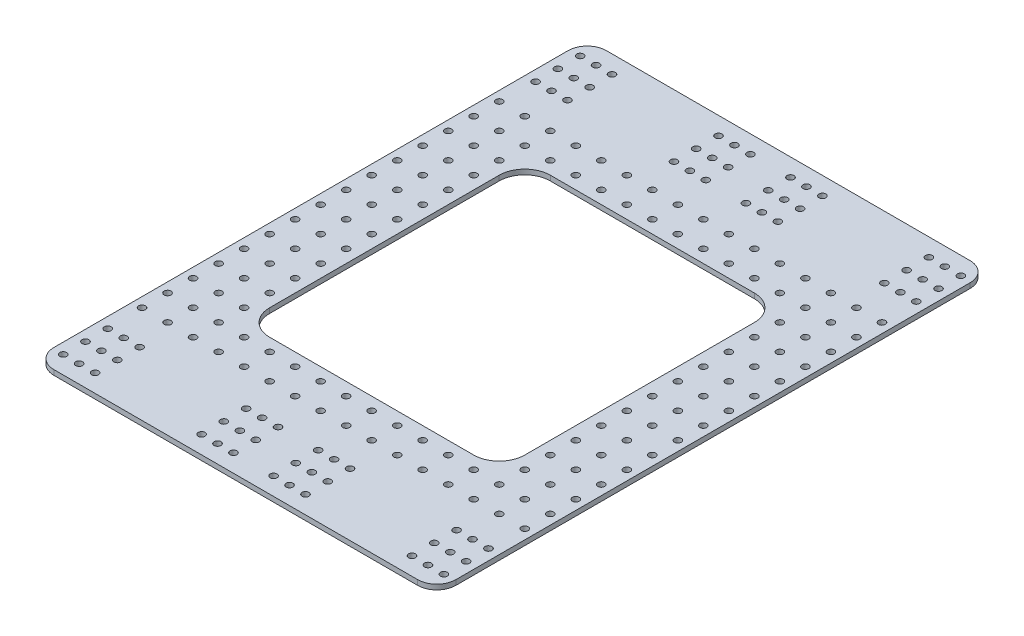
SolidWorks part; units mm, degrees
ref_plane "Front Plane" through (0, 0, 0) normal (0, 0, 1) x (1, 0, 0)
ref_plane "Top Plane" through (0, 0, 0) normal (0, 1, 0) x (1, 0, 0)
ref_plane "Right Plane" through (0, 0, 0) normal (1, 0, 0) x (0, 0, -1)
sketch "Sketch2" plane through (0, 50, 0) normal (0, 1, 0) x (1, 0, 0)
  line L6 (100.0588, 137.5) -> (-100.0588, 137.5)
  line L7 (100.0588, 137.5) -> (100.0588, -137.5)
  line L8 (100.0588, -137.5) -> (-100.0588, -137.5)
  line L9 (-100.0588, 137.5) -> (-100.0588, -137.5)
  line L10 (100.0588, 137.5) -> (-100.0588, -137.5) construction
  line L11 (100.0588, -137.5) -> (-100.0588, 137.5) construction
  point P0 (0, 0)
extrude "Boss-Extrude1" add sketch "Sketch2" along normal blind 2.5
sketch "Sketch4" plane through (0, 52.5, 0) normal (0, 1, 0) x (1, 0, 0)
  circle A0 centre (-9.9812, -128.65) radius 1.27 construction
  circle A1 centre (-9.9812, -106.4725) radius 1.27 construction
  circle A2 centre (-9.9812, -117.5612) radius 1.27 construction
  circle A3 centre (-17.9187, -117.5612) radius 1.27 construction
  circle A4 centre (-17.9187, -106.4725) radius 1.27 construction
  circle A5 centre (-25.8562, -106.4725) radius 1.27 construction
  circle A6 centre (-25.8562, -117.5612) radius 1.27 construction
  circle A7 centre (-17.9187, -128.65) radius 1.27 construction
  circle A8 centre (-25.8562, -128.65) radius 1.27 construction
  circle A9 centre (-86.8122, -117.5612) radius 1.27 construction
  circle A10 centre (-86.8122, -128.65) radius 1.27 construction
  circle A11 centre (-78.8747, -128.65) radius 1.27 construction
  circle A12 centre (-78.8747, -117.5612) radius 1.27 construction
  circle A13 centre (-78.8747, -106.4725) radius 1.27 construction
  circle A14 centre (-86.8122, -106.4725) radius 1.27 construction
  circle A15 centre (-94.7497, -106.4725) radius 1.27 construction
  circle A16 centre (-94.7497, -117.5612) radius 1.27 construction
  circle A17 centre (-94.7497, -128.65) radius 1.27 construction
  circle A18 centre (-9.9812, -128.65) radius 1.27 construction
  circle A19 centre (-9.9812, -106.4725) radius 1.27 construction
  circle A20 centre (-9.9812, -117.5612) radius 1.27 construction
  circle A21 centre (-17.9187, -117.5612) radius 1.27 construction
  circle A22 centre (-17.9187, -106.4725) radius 1.27 construction
  circle A23 centre (-25.8562, -106.4725) radius 1.27 construction
  circle A24 centre (-25.8562, -117.5612) radius 1.27 construction
  circle A25 centre (-17.9187, -128.65) radius 1.27 construction
  circle A26 centre (-25.8562, -128.65) radius 1.27 construction
  circle A27 centre (-86.8122, -117.5612) radius 1.27 construction
  circle A28 centre (-86.8122, -128.65) radius 1.27 construction
  circle A29 centre (-78.8747, -128.65) radius 1.27 construction
  circle A30 centre (-78.8747, -117.5612) radius 1.27 construction
  circle A31 centre (-78.8747, -106.4725) radius 1.27 construction
  circle A32 centre (-86.8122, -106.4725) radius 1.27 construction
  circle A33 centre (-94.7497, -106.4725) radius 1.27 construction
  circle A34 centre (-94.7497, -117.5612) radius 1.27 construction
  circle A35 centre (-94.7497, -128.65) radius 1.27 construction
hole_wizard "M3 Clearance Hole1" positions "3DSketch2" profile "Sketch6" hole size "M3" standard "ANSI Metric" end condition through all
sketch3d "3DSketch2"
  point P0 (-94.7497, 52.5, 106.4725)
  point P3 (-86.8122, 52.5, 106.4725)
  point P6 (-78.8747, 52.5, 106.4725)
  point P9 (-78.8747, 52.5, 117.5612)
  point P12 (-86.8122, 52.5, 117.5612)
  point P15 (-94.7497, 52.5, 117.5612)
  point P18 (-94.7497, 52.5, 128.65)
  point P21 (-86.8122, 52.5, 128.65)
  point P24 (-78.8747, 52.5, 128.65)
  point P27 (-25.8562, 52.5, 106.4725)
  point P30 (-17.9187, 52.5, 106.4725)
  point P33 (-9.9812, 52.5, 106.4725)
  point P35 (-9.9812, 52.5, 117.5612)
  point P38 (-17.9187, 52.5, 117.5612)
  point P41 (-25.8562, 52.5, 117.5612)
  point P44 (-25.8562, 52.5, 128.65)
  point P47 (-17.9187, 52.5, 128.65)
  point P50 (-9.9812, 52.5, 128.65)
sketch "Sketch6" plane through (-94.7497, 52.5, 106.4725) normal (1, 0, 0) x (0, 0, 1)
  line L0 (0, 0) -> (0, 2.5)
  line L1 (0, 2.5) -> (1.7, 2.5)
  line L2 (1.7, 2.5) -> (1.7, 0)
  line L5 (1.7, 0) -> (0, 0)
  line L11 (0, -6.35) -> (0, 107.95) construction
  dimension "Thru Hole Dia." = 3.4
  dimension "Thru Hole Depth" = 2.5
mirror "Mirror1" about plane through (0, 0, 0) normal (1, 0, 0) of "M3 Clearance Hole1"
mirror "Mirror2" about plane through (0, 0, 0) normal (0, 0, 1) of "M3 Clearance Hole1", "Mirror1"
fillet "Fillet1" radius 9.525 4 edges at (-100.0588, 51.25, -137.5) (100.0588, 51.25, 137.5) (-100.0588, 51.25, 137.5) (100.0588, 51.25, -137.5)
sketch "Sketch7" plane through (0, 52.5, 0) normal (0, 1, 0) x (1, 0, 0)
  line L1 (0, 0) -> (6.35, 0) construction
  line L2 (0, 0) -> (0, -6.35) construction
  line L3 (0, -6.35) -> (6.35, -6.35) construction
  line L4 (6.35, 0) -> (6.35, -6.35) construction
  point P6 (6.35, -6.35)
  dimension "D1" = 6.35
hole_wizard "M3 Clearance Hole2" positions "Sketch9" profile "Sketch10" hole size "M3" standard "ANSI Metric" end condition through all
sketch "Sketch9" plane through (0, 52.5, 0) normal (0, 1, 0) x (1, 0, 0)
  point P0 (6.35, 0)
sketch "Sketch10" plane through (6.35, 52.5, 0) normal (1, 0, 0) x (0, 0, 1)
  line L0 (0, 0) -> (0, 2.5)
  line L1 (0, 2.5) -> (1.7, 2.5)
  line L2 (1.7, 2.5) -> (1.7, 0)
  line L5 (1.7, 0) -> (0, 0)
  line L11 (0, -6.35) -> (0, 107.95) construction
  dimension "Thru Hole Dia." = 3.4
  dimension "Thru Hole Depth" = 2.5
pattern_linear "LPattern1" count 8 spacing 12.7 along (0, 0, 1) count 8 spacing 12.7 along (1, 0, 0) of "M3 Clearance Hole2"
mirror "Mirror3" about plane through (0, 0, 0) normal (0, 0, 1) of "LPattern1", "M3 Clearance Hole2"
mirror "Mirror4" about plane through (0, 0, 0) normal (1, 0, 0) of "Mirror3", "LPattern1", "M3 Clearance Hole2"
sketch "Sketch11" plane through (0, 52.5, 0) normal (0, 1, 0) x (1, 0, 0)
  line L0 (69.85, -63.5) -> (57.15, -76.2) construction
  line L1 (-63.5, 69.85) -> (63.5, 69.85)
  line L2 (-63.5, 69.85) -> (-63.5, -69.85)
  line L3 (-63.5, -69.85) -> (63.5, -69.85)
  line L4 (63.5, 69.85) -> (63.5, -69.85)
  line L5 (-63.5, 69.85) -> (63.5, -69.85) construction
  line L6 (-63.5, -69.85) -> (63.5, 69.85) construction
  point P0 (0, 0)
  point P10 (63.5, -69.85)
extrude "Cut-Extrude1" cut sketch "Sketch11" against normal through all
fillet "Fillet2" radius 12.7 4 edges at (-63.5, 51.25, -69.85) (-63.5, 51.25, 69.85) (63.5, 51.25, 69.85) (63.5, 51.25, -69.85)
